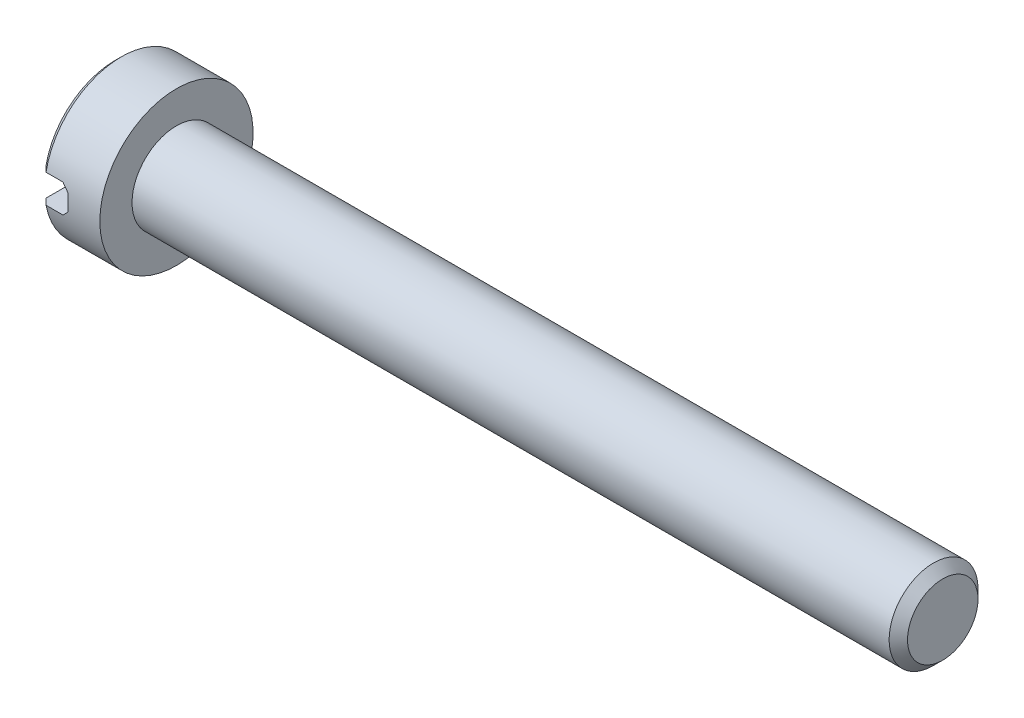
SolidWorks part; units mm, degrees
ref_plane "Face" through (0, 0, 0) normal (0, 0, 1) x (1, 0, 0)
ref_plane "Dessus" through (0, 0, 0) normal (0, 1, 0) x (1, 0, 0)
ref_plane "Droite" through (0, 0, 0) normal (1, 0, 0) x (0, 0, -1)
sketch "Esquisse1" plane through (0, 0, 0) normal (0, 0, 1) x (1, 0, 0)
  line L0 (0, 0) -> (0, 2.3)
  line L1 (0.2, 2.5) -> (2, 2.5)
  line L2 (2, 2.5) -> (2, 0)
  line L5 (0, 0) -> (7.6423, 0) construction
  line L7 (0, 2.3) -> (0.2, 2.5)
  line L8 (0, 0) -> (2, 0)
  point P1 (0, 2.5)
  dimension "D1" = 2.5
  dimension "D3" = 2
  dimension "D9" = 0.2
revolve "Révolution1" add sketch "Esquisse1" angle 360 about L5
sketch "Esquisse2" plane through (0, 0, 0) normal (0, 0, 1) x (1, 0, 0)
  line L0 (0, 2.3) -> (0, -2.3) construction
  line L1 (0, 0.4655) -> (0.7534, 0.4655)
  line L2 (0, 0.4655) -> (0, -0.4655)
  line L3 (0, -0.4655) -> (0.7534, -0.4655)
  line L4 (0.9534, 0.2655) -> (0.9534, -0.2655)
  line L5 (0.7534, 0.4655) -> (0.9534, 0.2655)
  line L6 (0.7534, -0.4655) -> (0.9534, -0.2655)
  point P1 (0.9534, -0.4655)
  point P3 (0.9534, 0.4655)
  dimension "D3" = 0.2
  dimension "D4" = 0.2
extrude "Enlèv. mat.-Extru.1" cut sketch "Esquisse2" against normal mid plane 10
sketch "Esquisse3" plane through (2, 0, 0) normal (1, 0, 0) x (0, 0, -1)
  circle A0 centre (0, 0) radius 1.45
extrude "Extrusion1" add sketch "Esquisse3" along normal blind 25
chamfer "Chanfrein1" distance 0.3 angle 45 1 edges at (27, 0, -1.45)
